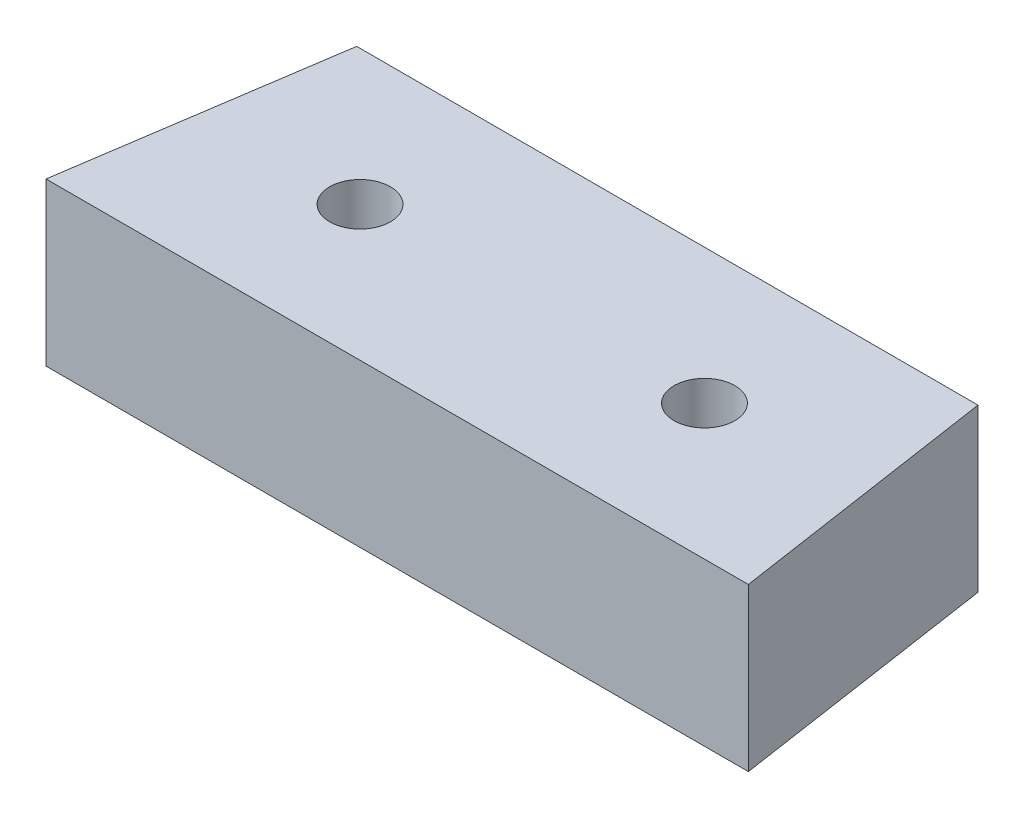
SolidWorks part; units mm, degrees
ref_plane "Front Plane" through (0, 0, 0) normal (0, 0, 1) x (1, 0, 0)
ref_plane "Top Plane" through (0, 0, 0) normal (0, 1, 0) x (1, 0, 0)
ref_plane "Right Plane" through (0, 0, 0) normal (1, 0, 0) x (0, 0, -1)
sketch "Sketch1" plane through (0, 0, 0) normal (0, 1, 0) x (1, 0, 0)
  line L0 (-23, 10) -> (-26, -10)
  line L1 (23, -10) -> (-23, -10) construction
  line L2 (23, -10) -> (23, 10) construction
  line L3 (23, 10) -> (-23, 10)
  line L4 (-23, -10) -> (-23, 10) construction
  line L5 (23, -10) -> (-23, 10) construction
  line L6 (23, 10) -> (-23, -10) construction
  line L7 (-26, -10) -> (26, -10)
  line L8 (26, -10) -> (23, 10)
  line L9 (-12.75, 0) -> (12.75, 0) construction
  circle A0 centre (-12.75, 0) radius 2.25
  circle A1 centre (12.75, 0) radius 2.25
  point P0 (0, 0)
  point P12 (0, 0)
  dimension "D4" = 4.5
  dimension "D1" = 46
  dimension "D2" = 20
  dimension "D3" = 52
  dimension "D5" = 25.5
extrude "Boss-Extrude1" add sketch "Sketch1" along normal blind 12
